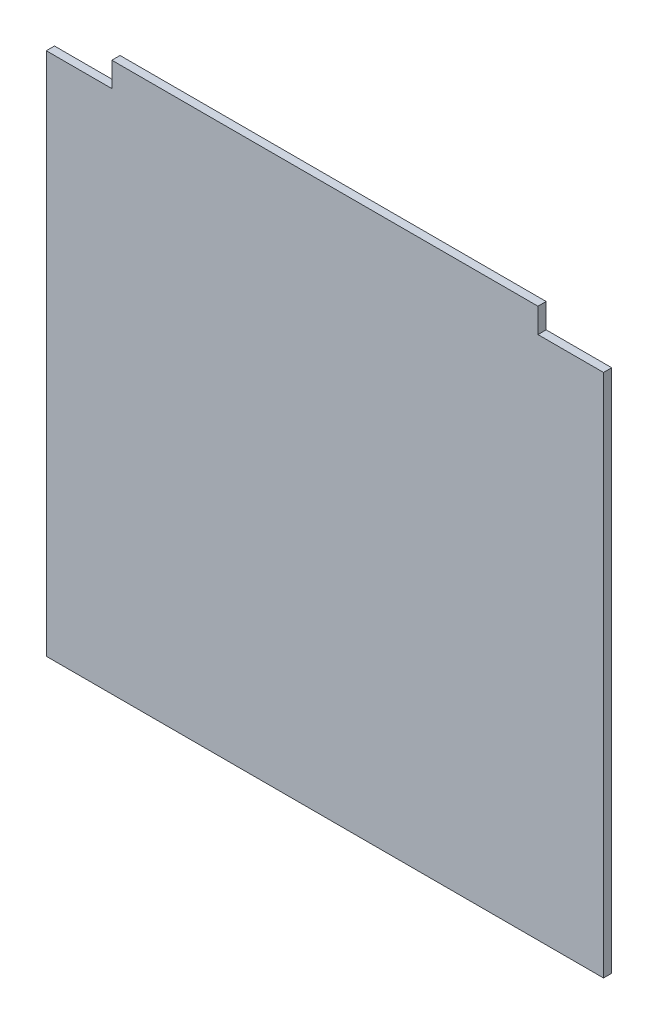
SolidWorks part; units mm, degrees
ref_plane "Plan de face" through (0, 0, 0) normal (0, 0, 1) x (1, 0, 0)
ref_plane "Plan de dessus" through (0, 0, 0) normal (0, 1, 0) x (1, 0, 0)
ref_plane "Plan de droite" through (0, 0, 0) normal (1, 0, 0) x (0, 0, -1)
sketch "Esquisse1" plane through (0, 0, 0) normal (0, 0, 1) x (1, 0, 0)
  line L1 (-340, 335) -> (340, 335)
  line L2 (-340, 335) -> (-340, -335)
  line L3 (-340, -335) -> (340, -335)
  line L4 (340, 335) -> (340, -335)
  dimension "D1" = 680
  dimension "D2" = 340
  dimension "D3" = 670
  dimension "D4" = 335
extrude "Boss.-Extru.1" add sketch "Esquisse1" along normal blind 10
sketch "Esquisse2" plane through (0, 0, 10) normal (0, 0, 1) x (1, 0, 0)
  line L0 (340, 335) -> (-340, 335) construction
  line L1 (-340, 335) -> (-260, 335)
  line L2 (-340, 335) -> (-340, 305)
  line L3 (-340, 305) -> (-260, 305)
  line L4 (-260, 335) -> (-260, 305)
  line L5 (340, 335) -> (260, 335)
  line L6 (340, 335) -> (340, 305)
  line L7 (340, 305) -> (260, 305)
  line L8 (260, 335) -> (260, 305)
  dimension "D1" = 30
  dimension "D2" = 30
  dimension "D3" = 80
  dimension "D4" = 80
extrude "Enlèv. mat.-Extru.1" cut sketch "Esquisse2" against normal through all
